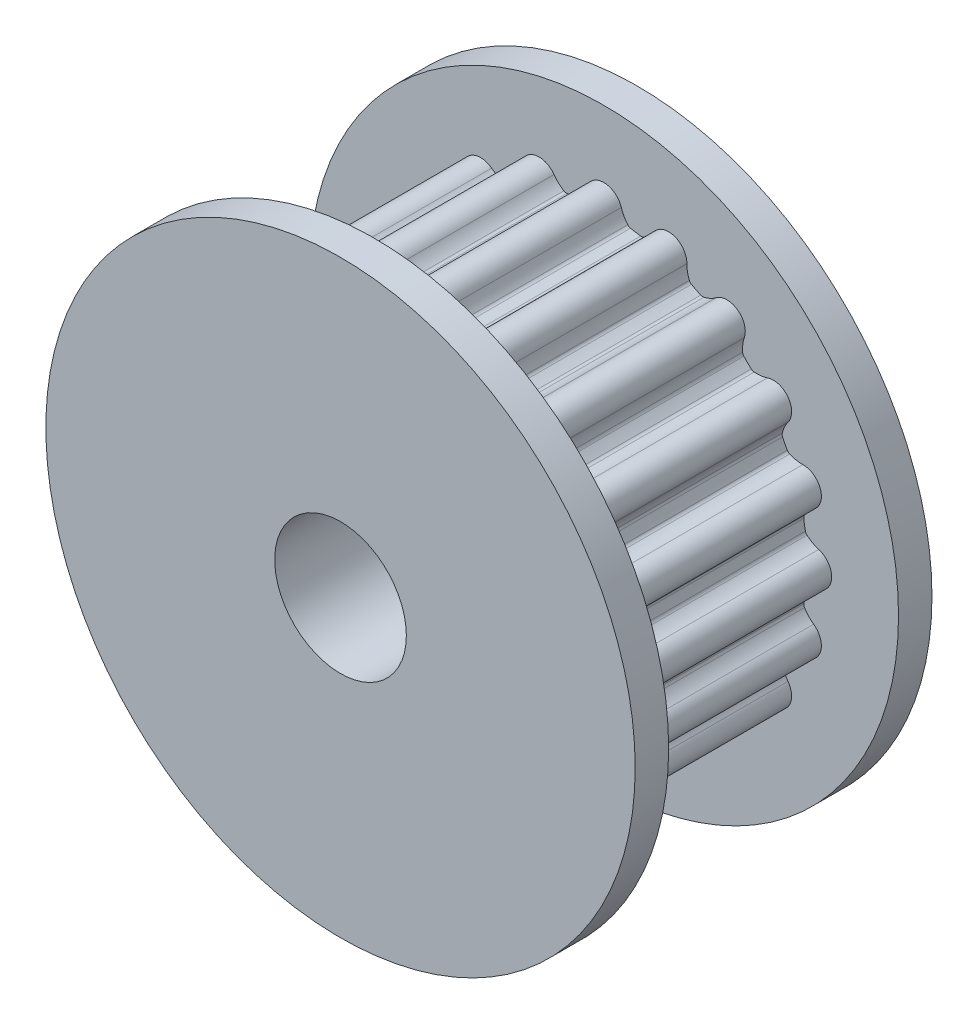
SolidWorks part; units mm, degrees
ref_plane "Front Plane" through (0, 0, 0) normal (0, 0, 1) x (1, 0, 0)
ref_plane "Top Plane" through (0, 0, 0) normal (0, 1, 0) x (1, 0, 0)
ref_plane "Right Plane" through (0, 0, 0) normal (1, 0, 0) x (0, 0, -1)
sketch "Sketch1" plane through (0, 0, 0) normal (0, 0, 1) x (1, 0, 0)
  circle A0 centre (0, 0) radius 8.9535
  circle A1 centre (0, 0) radius 2
  dimension "D1" = 17.907
  dimension "D2" = 4
extrude "Boss-Extrude1" add sketch "Sketch1" along normal blind 1.016
sketch "Sketch2" plane through (0, 0, 1.016) normal (0, 0, 1) x (1, 0, 0)
  line L0 (0, 6.3662) -> (0, 0) construction
  line L1 (0, 0) -> (1.9673, 6.0546) construction
  line L5 (0.9654, 6.0952) -> (0, 0) construction
  arc A1 (0.5303, 6.5298) -> (0, 6.9212) centre (0, 6.3662) ccw
  arc A3 (2.1388, 6.5825) -> (1.5134, 6.3741) centre (1.9673, 6.0546) ccw
  arc A18 (0.7273, 6.173) -> (0.81, 6.124) centre (0.8411, 6.2707) ccw
  arc A19 (1.1221, 6.0746) -> (1.2158, 6.0956) centre (1.1378, 6.2237) ccw
  arc A20 (0, 6.9212) -> (2.1388, 6.5825) centre (0, 0) cw construction
  arc A21 (0.81, 6.124) -> (1.1221, 6.0746) centre (1.4394, 9.0877) ccw
  arc A22 (0, 6.3662) -> (1.9673, 6.0546) centre (0, 0) cw construction
  arc A23 (2.5222, 6.0463) -> (2.1388, 6.5825) centre (1.9673, 6.0546) ccw
  arc A24 (0.5303, 6.5298) -> (0.7273, 6.173) centre (1.4859, 6.8246) ccw
  arc A25 (1.5134, 6.3741) -> (1.2158, 6.0956) centre (0.6957, 6.9498) cw
  arc A26 (2.5222, 6.0463) -> (2.5993, 5.6461) centre (3.5221, 6.0314) ccw
  arc A27 (2.5993, 5.6461) -> (2.6627, 5.574) centre (2.7377, 5.7039) ccw
  arc A28 (2.6627, 5.574) -> (2.9443, 5.4305) centre (4.1772, 8.1981) ccw
  arc A29 (2.9443, 5.4305) -> (3.04, 5.4216) centre (3.0054, 5.5675) ccw
  arc A30 (3.4091, 5.5944) -> (3.04, 5.4216) centre (2.8093, 6.3946) cw
  arc A31 (4.0682, 5.5994) -> (3.4091, 5.5944) centre (3.742, 5.1504) ccw
  arc A32 (4.2672, 4.971) -> (4.0682, 5.5994) centre (3.742, 5.1504) ccw
  arc A33 (4.2672, 4.971) -> (4.2168, 4.5665) centre (5.2135, 4.6478) ccw
  arc A34 (4.2168, 4.5665) -> (4.2549, 4.4783) centre (4.3663, 4.5787) ccw
  arc A35 (4.2549, 4.4783) -> (4.4783, 4.2549) centre (6.5061, 6.5061) ccw
  arc A36 (4.4783, 4.2549) -> (4.5665, 4.2168) centre (4.5787, 4.3663) ccw
  arc A37 (4.971, 4.2672) -> (4.5665, 4.2168) centre (4.6478, 5.2135) cw
  arc A38 (5.5994, 4.0682) -> (4.971, 4.2672) centre (5.1504, 3.742) ccw
  arc A39 (5.5944, 3.4091) -> (5.5994, 4.0682) centre (5.1504, 3.742) ccw
  arc A40 (5.5944, 3.4091) -> (5.4216, 3.04) centre (6.3946, 2.8093) ccw
  arc A41 (5.4216, 3.04) -> (5.4305, 2.9443) centre (5.5675, 3.0054) ccw
  arc A42 (5.4305, 2.9443) -> (5.574, 2.6627) centre (8.1981, 4.1772) ccw
  arc A43 (5.574, 2.6627) -> (5.6461, 2.5993) centre (5.7039, 2.7377) ccw
  arc A44 (6.0463, 2.5222) -> (5.6461, 2.5993) centre (6.0314, 3.5221) cw
  arc A45 (6.5825, 2.1388) -> (6.0463, 2.5222) centre (6.0546, 1.9673) ccw
  arc A46 (6.3741, 1.5134) -> (6.5825, 2.1388) centre (6.0546, 1.9673) ccw
  arc A47 (6.3741, 1.5134) -> (6.0956, 1.2158) centre (6.9498, 0.6957) ccw
  arc A48 (6.0956, 1.2158) -> (6.0746, 1.1221) centre (6.2237, 1.1378) ccw
  arc A49 (6.0746, 1.1221) -> (6.124, 0.81) centre (9.0877, 1.4394) ccw
  arc A50 (6.124, 0.81) -> (6.173, 0.7273) centre (6.2707, 0.8411) ccw
  arc A51 (6.5298, 0.5303) -> (6.173, 0.7273) centre (6.8246, 1.4859) cw
  arc A52 (6.9212, 0) -> (6.5298, 0.5303) centre (6.3662, 0) ccw
  arc A53 (6.5298, -0.5303) -> (6.9212, 0) centre (6.3662, 0) ccw
  arc A54 (6.5298, -0.5303) -> (6.173, -0.7273) centre (6.8246, -1.4859) ccw
  arc A55 (6.173, -0.7273) -> (6.124, -0.81) centre (6.2707, -0.8411) ccw
  arc A56 (6.124, -0.81) -> (6.0746, -1.1221) centre (9.0877, -1.4394) ccw
  arc A57 (6.0746, -1.1221) -> (6.0956, -1.2158) centre (6.2237, -1.1378) ccw
  arc A58 (6.3741, -1.5134) -> (6.0956, -1.2158) centre (6.9498, -0.6957) cw
  arc A59 (6.5825, -2.1388) -> (6.3741, -1.5134) centre (6.0546, -1.9673) ccw
  arc A60 (6.0463, -2.5222) -> (6.5825, -2.1388) centre (6.0546, -1.9673) ccw
  arc A61 (6.0463, -2.5222) -> (5.6461, -2.5993) centre (6.0314, -3.5221) ccw
  arc A62 (5.6461, -2.5993) -> (5.574, -2.6627) centre (5.7039, -2.7377) ccw
  arc A63 (5.574, -2.6627) -> (5.4305, -2.9443) centre (8.1981, -4.1772) ccw
  arc A64 (5.4305, -2.9443) -> (5.4216, -3.04) centre (5.5675, -3.0054) ccw
  arc A65 (5.5944, -3.4091) -> (5.4216, -3.04) centre (6.3946, -2.8093) cw
  arc A66 (5.5994, -4.0682) -> (5.5944, -3.4091) centre (5.1504, -3.742) ccw
  arc A67 (4.971, -4.2672) -> (5.5994, -4.0682) centre (5.1504, -3.742) ccw
  arc A68 (4.971, -4.2672) -> (4.5665, -4.2168) centre (4.6478, -5.2135) ccw
  arc A69 (4.5665, -4.2168) -> (4.4783, -4.2549) centre (4.5787, -4.3663) ccw
  arc A70 (4.4783, -4.2549) -> (4.2549, -4.4783) centre (6.5061, -6.5061) ccw
  arc A71 (4.2549, -4.4783) -> (4.2168, -4.5665) centre (4.3663, -4.5787) ccw
  arc A72 (4.2672, -4.971) -> (4.2168, -4.5665) centre (5.2135, -4.6478) cw
  arc A73 (4.0682, -5.5994) -> (4.2672, -4.971) centre (3.742, -5.1504) ccw
  arc A74 (3.4091, -5.5944) -> (4.0682, -5.5994) centre (3.742, -5.1504) ccw
  arc A75 (3.4091, -5.5944) -> (3.04, -5.4216) centre (2.8093, -6.3946) ccw
  arc A76 (3.04, -5.4216) -> (2.9443, -5.4305) centre (3.0054, -5.5675) ccw
  arc A77 (2.9443, -5.4305) -> (2.6627, -5.574) centre (4.1772, -8.1981) ccw
  arc A78 (2.6627, -5.574) -> (2.5993, -5.6461) centre (2.7377, -5.7039) ccw
  arc A79 (2.5222, -6.0463) -> (2.5993, -5.6461) centre (3.5221, -6.0314) cw
  arc A80 (2.1388, -6.5825) -> (2.5222, -6.0463) centre (1.9673, -6.0546) ccw
  arc A81 (1.5134, -6.3741) -> (2.1388, -6.5825) centre (1.9673, -6.0546) ccw
  arc A82 (1.5134, -6.3741) -> (1.2158, -6.0956) centre (0.6957, -6.9498) ccw
  arc A83 (1.2158, -6.0956) -> (1.1221, -6.0746) centre (1.1378, -6.2237) ccw
  arc A84 (1.1221, -6.0746) -> (0.81, -6.124) centre (1.4394, -9.0877) ccw
  arc A85 (0.81, -6.124) -> (0.7273, -6.173) centre (0.8411, -6.2707) ccw
  arc A86 (0.5303, -6.5298) -> (0.7273, -6.173) centre (1.4859, -6.8246) cw
  arc A87 (0, -6.9212) -> (0.5303, -6.5298) centre (0, -6.3662) ccw
  arc A88 (-0.5303, -6.5298) -> (0, -6.9212) centre (0, -6.3662) ccw
  arc A89 (-0.5303, -6.5298) -> (-0.7273, -6.173) centre (-1.4859, -6.8246) ccw
  arc A90 (-0.7273, -6.173) -> (-0.81, -6.124) centre (-0.8411, -6.2707) ccw
  arc A91 (-0.81, -6.124) -> (-1.1221, -6.0746) centre (-1.4394, -9.0877) ccw
  arc A92 (-1.1221, -6.0746) -> (-1.2158, -6.0956) centre (-1.1378, -6.2237) ccw
  arc A93 (-1.5134, -6.3741) -> (-1.2158, -6.0956) centre (-0.6957, -6.9498) cw
  arc A94 (-2.1388, -6.5825) -> (-1.5134, -6.3741) centre (-1.9673, -6.0546) ccw
  arc A95 (-2.5222, -6.0463) -> (-2.1388, -6.5825) centre (-1.9673, -6.0546) ccw
  arc A96 (-2.5222, -6.0463) -> (-2.5993, -5.6461) centre (-3.5221, -6.0314) ccw
  arc A97 (-2.5993, -5.6461) -> (-2.6627, -5.574) centre (-2.7377, -5.7039) ccw
  arc A98 (-2.6627, -5.574) -> (-2.9443, -5.4305) centre (-4.1772, -8.1981) ccw
  arc A99 (-2.9443, -5.4305) -> (-3.04, -5.4216) centre (-3.0054, -5.5675) ccw
  arc A100 (-3.4091, -5.5944) -> (-3.04, -5.4216) centre (-2.8093, -6.3946) cw
  arc A101 (-4.0682, -5.5994) -> (-3.4091, -5.5944) centre (-3.742, -5.1504) ccw
  arc A102 (-4.2672, -4.971) -> (-4.0682, -5.5994) centre (-3.742, -5.1504) ccw
  arc A103 (-4.2672, -4.971) -> (-4.2168, -4.5665) centre (-5.2135, -4.6478) ccw
  arc A104 (-4.2168, -4.5665) -> (-4.2549, -4.4783) centre (-4.3663, -4.5787) ccw
  arc A105 (-4.2549, -4.4783) -> (-4.4783, -4.2549) centre (-6.5061, -6.5061) ccw
  arc A106 (-4.4783, -4.2549) -> (-4.5665, -4.2168) centre (-4.5787, -4.3663) ccw
  arc A107 (-4.971, -4.2672) -> (-4.5665, -4.2168) centre (-4.6478, -5.2135) cw
  arc A108 (-5.5994, -4.0682) -> (-4.971, -4.2672) centre (-5.1504, -3.742) ccw
  arc A109 (-5.5944, -3.4091) -> (-5.5994, -4.0682) centre (-5.1504, -3.742) ccw
  arc A110 (-5.5944, -3.4091) -> (-5.4216, -3.04) centre (-6.3946, -2.8093) ccw
  arc A111 (-5.4216, -3.04) -> (-5.4305, -2.9443) centre (-5.5675, -3.0054) ccw
  arc A112 (-5.4305, -2.9443) -> (-5.574, -2.6627) centre (-8.1981, -4.1772) ccw
  arc A113 (-5.574, -2.6627) -> (-5.6461, -2.5993) centre (-5.7039, -2.7377) ccw
  arc A114 (-6.0463, -2.5222) -> (-5.6461, -2.5993) centre (-6.0314, -3.5221) cw
  arc A115 (-6.5825, -2.1388) -> (-6.0463, -2.5222) centre (-6.0546, -1.9673) ccw
  arc A116 (-6.3741, -1.5134) -> (-6.5825, -2.1388) centre (-6.0546, -1.9673) ccw
  arc A117 (-6.3741, -1.5134) -> (-6.0956, -1.2158) centre (-6.9498, -0.6957) ccw
  arc A118 (-6.0956, -1.2158) -> (-6.0746, -1.1221) centre (-6.2237, -1.1378) ccw
  arc A119 (-6.0746, -1.1221) -> (-6.124, -0.81) centre (-9.0877, -1.4394) ccw
  arc A120 (-6.124, -0.81) -> (-6.173, -0.7273) centre (-6.2707, -0.8411) ccw
  arc A121 (-6.5298, -0.5303) -> (-6.173, -0.7273) centre (-6.8246, -1.4859) cw
  arc A122 (-6.9212, 0) -> (-6.5298, -0.5303) centre (-6.3662, 0) ccw
  arc A123 (-6.5298, 0.5303) -> (-6.9212, 0) centre (-6.3662, 0) ccw
  arc A124 (-6.5298, 0.5303) -> (-6.173, 0.7273) centre (-6.8246, 1.4859) ccw
  arc A125 (-6.173, 0.7273) -> (-6.124, 0.81) centre (-6.2707, 0.8411) ccw
  arc A126 (-6.124, 0.81) -> (-6.0746, 1.1221) centre (-9.0877, 1.4394) ccw
  arc A127 (-6.0746, 1.1221) -> (-6.0956, 1.2158) centre (-6.2237, 1.1378) ccw
  arc A128 (-6.3741, 1.5134) -> (-6.0956, 1.2158) centre (-6.9498, 0.6957) cw
  arc A129 (-6.5825, 2.1388) -> (-6.3741, 1.5134) centre (-6.0546, 1.9673) ccw
  arc A130 (-6.0463, 2.5222) -> (-6.5825, 2.1388) centre (-6.0546, 1.9673) ccw
  arc A131 (-6.0463, 2.5222) -> (-5.6461, 2.5993) centre (-6.0314, 3.5221) ccw
  arc A132 (-5.6461, 2.5993) -> (-5.574, 2.6627) centre (-5.7039, 2.7377) ccw
  arc A133 (-5.574, 2.6627) -> (-5.4305, 2.9443) centre (-8.1981, 4.1772) ccw
  arc A134 (-5.4305, 2.9443) -> (-5.4216, 3.04) centre (-5.5675, 3.0054) ccw
  arc A135 (-5.5944, 3.4091) -> (-5.4216, 3.04) centre (-6.3946, 2.8093) cw
  arc A136 (-5.5994, 4.0682) -> (-5.5944, 3.4091) centre (-5.1504, 3.742) ccw
  arc A137 (-4.971, 4.2672) -> (-5.5994, 4.0682) centre (-5.1504, 3.742) ccw
  arc A138 (-4.971, 4.2672) -> (-4.5665, 4.2168) centre (-4.6478, 5.2135) ccw
  arc A139 (-4.5665, 4.2168) -> (-4.4783, 4.2549) centre (-4.5787, 4.3663) ccw
  arc A140 (-4.4783, 4.2549) -> (-4.2549, 4.4783) centre (-6.5061, 6.5061) ccw
  arc A141 (-4.2549, 4.4783) -> (-4.2168, 4.5665) centre (-4.3663, 4.5787) ccw
  arc A142 (-4.2672, 4.971) -> (-4.2168, 4.5665) centre (-5.2135, 4.6478) cw
  arc A143 (-4.0682, 5.5994) -> (-4.2672, 4.971) centre (-3.742, 5.1504) ccw
  arc A144 (-3.4091, 5.5944) -> (-4.0682, 5.5994) centre (-3.742, 5.1504) ccw
  arc A145 (-3.4091, 5.5944) -> (-3.04, 5.4216) centre (-2.8093, 6.3946) ccw
  arc A146 (-3.04, 5.4216) -> (-2.9443, 5.4305) centre (-3.0054, 5.5675) ccw
  arc A147 (-2.9443, 5.4305) -> (-2.6627, 5.574) centre (-4.1772, 8.1981) ccw
  arc A148 (-2.6627, 5.574) -> (-2.5993, 5.6461) centre (-2.7377, 5.7039) ccw
  arc A149 (-2.5222, 6.0463) -> (-2.5993, 5.6461) centre (-3.5221, 6.0314) cw
  arc A150 (-2.1388, 6.5825) -> (-2.5222, 6.0463) centre (-1.9673, 6.0546) ccw
  arc A151 (-1.5134, 6.3741) -> (-2.1388, 6.5825) centre (-1.9673, 6.0546) ccw
  arc A152 (-1.5134, 6.3741) -> (-1.2158, 6.0956) centre (-0.6957, 6.9498) ccw
  arc A153 (-1.2158, 6.0956) -> (-1.1221, 6.0746) centre (-1.1378, 6.2237) ccw
  arc A154 (-1.1221, 6.0746) -> (-0.81, 6.124) centre (-1.4394, 9.0877) ccw
  arc A155 (-0.81, 6.124) -> (-0.7273, 6.173) centre (-0.8411, 6.2707) ccw
  arc A156 (-0.5303, 6.5298) -> (-0.7273, 6.173) centre (-1.4859, 6.8246) cw
  arc A157 (0, 6.9212) -> (-0.5303, 6.5298) centre (0, 6.3662) ccw
  circle A158 centre (0, 0) radius 2 construction
  circle A159 centre (0, 0) radius 2
  point P12 (0.9654, 6.0952)
  point P14 (1.0827, 6.836)
  point P40 (0, 0)
  point P309 (0, 0)
  dimension "D1" = 0.75
  dimension "D2" = 2
  dimension "D5" = 0.15
  dimension "D4" = 20
  dimension "D6" = 0.4
  dimension "D3" = 1
  dimension "D7" = 3.0298
  dimension "D8" = 0.555
extrude "Boss-Extrude2" add sketch "Sketch2" along normal blind 6.985
sketch "Sketch3" plane through (0, 0, 8.001) normal (0, 0, 1) x (1, 0, 0)
  circle A1 centre (0, 0) radius 8.9535
  circle A2 centre (0, 0) radius 8.9535
  circle A4 centre (0, 0) radius 2 construction
  circle A5 centre (0, 0) radius 2
  dimension "D1" = 0
extrude "Boss-Extrude3" add sketch "Sketch3" along normal blind 1.016
